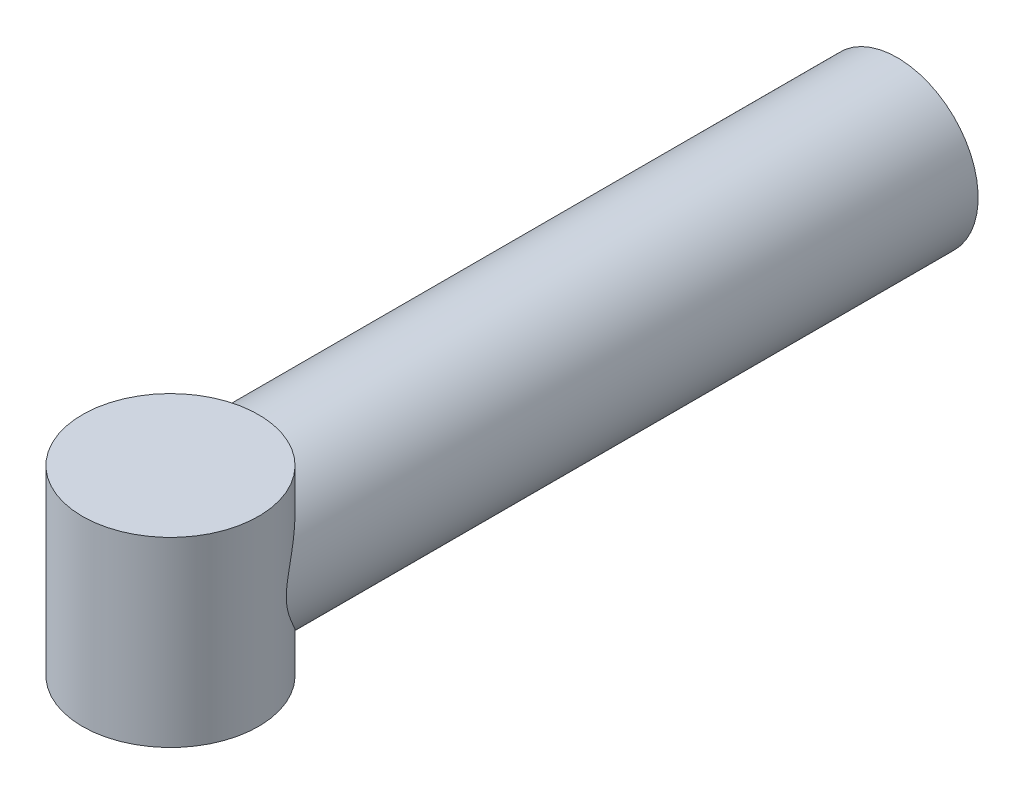
SolidWorks part; units mm, degrees
material "Ti-6Al-2Sn-2Zr-2Mo-2Cr-0.25Si (SS)"
ref_plane "Front Plane" through (0, 0, 0) normal (0, 0, 1) x (1, 0, 0)
ref_plane "Top Plane" through (0, 0, 0) normal (0, 1, 0) x (1, 0, 0)
ref_plane "Right Plane" through (0, 0, 0) normal (1, 0, 0) x (0, 0, -1)
sketch "Sketch1" plane through (0, 0, 0) normal (0, 0, 1) x (1, 0, 0)
  circle A0 centre (0, 0) radius 15
  circle A1 centre (0, 0) radius 20
  dimension "D1" = 40
  dimension "D2" = 30
extrude "Boss-Extrude1" add sketch "Sketch1" along normal blind 80
ref_plane "Plane1" through (0, 0, 80) normal (0, 0, 1) x (1, 0, 0)
sketch "Sketch3" plane through (0, 0, 80) normal (0, 0, 1) x (1, 0, 0)
  circle A1 centre (0, 0) radius 25
  dimension "D1" = 50
sketch "Sketch7" plane through (0, 0, 0) normal (0, 0, -1) x (-1, 0, 0)
  circle A0 centre (0, 0) radius 15
  circle A1 centre (0, 0) radius 20
extrude "Boss-Extrude4" add sketch "Sketch7" along normal blind 100
sketch "Sketch8" plane through (0, 0, 0) normal (0, 1, 0) x (1, 0, 0)
  circle A0 centre (0, -79.7384) radius 21.7898
extrude "Boss-Extrude5" add sketch "Sketch8" along normal mid plane 45
